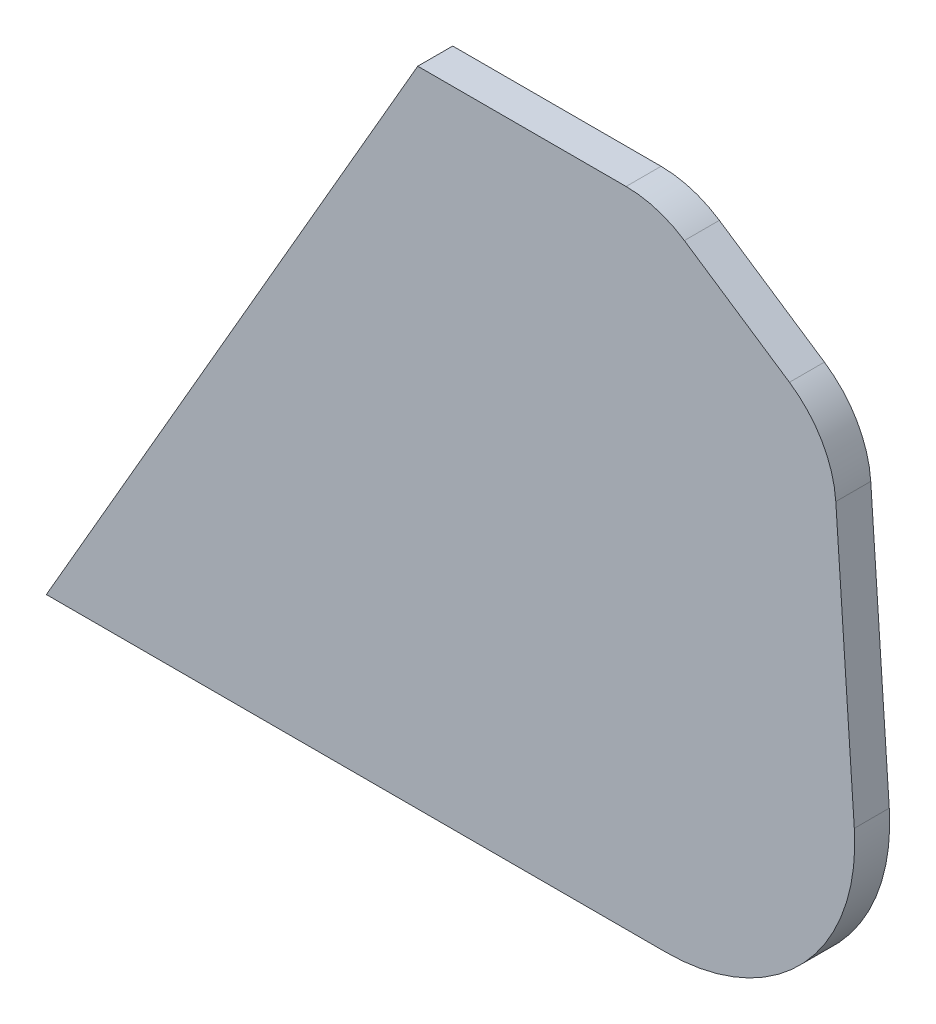
SolidWorks part; units mm, degrees
material "2024 Alloy"
ref_plane "Plane1" through (0, 0, 0) normal (0, 0, 1) x (1, 0, 0)
ref_plane "Plane2" through (0, 0, 0) normal (0, 1, 0) x (1, 0, 0)
ref_plane "Plane3" through (0, 0, 0) normal (1, 0, 0) x (0, 0, -1)
sketch "Sketch2" plane through (0, 0, 0) normal (0, 0, 1) x (1, 0, 0)
  line L1 (-2.1132, 5) -> (-5, 0) construction
  line L2 (48.1162, 92) -> (-5, 0)
  line L12 (110.5505, 28.8221) -> (107.9026, 67.9688)
  line L13 (101.2729, 79.4269) -> (86.2483, 89.4704)
  line L14 (77.9123, 92) -> (47.4641, 92)
  line L15 (47.4641, 92) -> (44, 86)
  line L16 (44, 86) -> (48.3301, 83.5)
  line L17 (48.3301, 83.5) -> (50.3509, 87)
  line L18 (50.3509, 87) -> (77.9123, 87)
  line L19 (83.4696, 85.3136) -> (98.4942, 75.2701)
  line L20 (102.914, 67.6314) -> (105.5619, 28.4847)
  line L21 (83.612, 5) -> (-2.1132, 5)
  line L22 (-2.1132, 5) -> (-5, 0)
  line L23 (-5, 0) -> (83.612, 0)
  line L24 (110.5505, 28.8221) -> (107.9026, 67.9688)
  line L25 (101.2729, 79.4269) -> (86.2483, 89.4704)
  line L26 (77.9123, 92) -> (48.1162, 92)
  line L35 (-5, 0) -> (83.612, 0)
  arc A6 (107.9026, 67.9688) -> (101.2729, 79.4269) centre (92.9368, 66.9566) ccw
  arc A7 (86.2483, 89.4704) -> (77.9123, 92) centre (77.9123, 77) ccw
  arc A8 (83.4696, 85.3136) -> (77.9123, 87) centre (77.9123, 77) ccw
  arc A9 (102.914, 67.6314) -> (98.4942, 75.2701) centre (92.9368, 66.9566) ccw
  arc A10 (83.612, 5) -> (105.5619, 28.4847) centre (83.612, 27) ccw
  arc A11 (83.612, 0) -> (110.5505, 28.8221) centre (83.612, 27) ccw
  arc A12 (107.9026, 67.9688) -> (101.2729, 79.4269) centre (92.9368, 66.9566) ccw
  arc A13 (86.2483, 89.4704) -> (77.9123, 92) centre (77.9123, 77) ccw
  arc A17 (83.612, 0) -> (110.5505, 28.8221) centre (83.612, 27) ccw
  dimension "D1" = 0
extrude "Base-Extrude" add sketch "Sketch2" along normal blind 5
